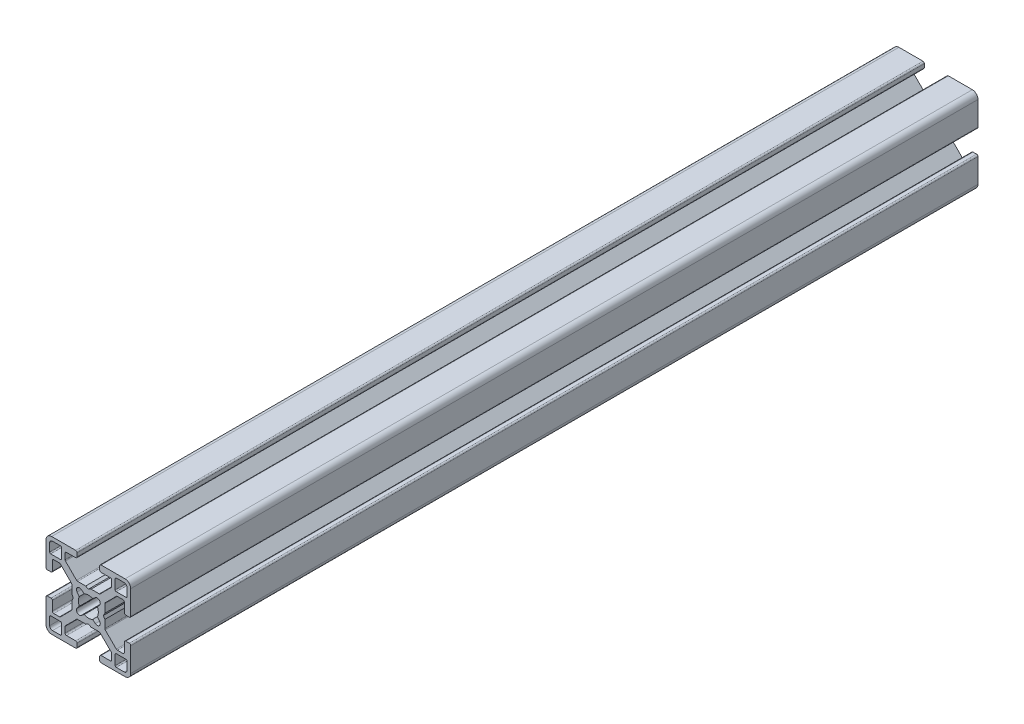
SolidWorks part; units mm, degrees
material "6105-T5 Aluminum"
ref_plane "Front Plane" through (0, 0, 0) normal (0, 0, 1) x (1, 0, 0)
ref_plane "Top Plane" through (0, 0, 0) normal (0, 1, 0) x (1, 0, 0)
ref_plane "Right Plane" through (0, 0, 0) normal (1, 0, 0) x (0, 0, -1)
sketch "Sketch1" plane through (0, 0, 0) normal (0, 0, 1) x (1, 0, 0)
  line L0 (9.5, -13.3189) -> (9.5, -9.88)
  line L1 (9.88, -9.5) -> (13.3189, -9.5)
  line L2 (13.6999, -9.881) -> (13.6999, -12.6999)
  line L3 (12.6999, -13.6999) -> (9.881, -13.6999)
  line L4 (-13.3189, -9.5) -> (-9.88, -9.5)
  line L5 (-9.5, -9.88) -> (-9.5, -13.3189)
  line L6 (-9.881, -13.6999) -> (-12.6999, -13.6999)
  line L7 (-13.6999, -12.6999) -> (-13.6999, -9.881)
  line L8 (-1.4942, -3.1981) -> (-2.4733, -3.9799)
  line L9 (-3.9799, -2.4733) -> (-3.1981, -1.4942)
  line L10 (-3.1981, 1.4942) -> (-3.9799, 2.4733)
  line L11 (-2.4733, 3.9799) -> (-1.4942, 3.1981)
  line L12 (1.4942, 3.1981) -> (2.4733, 3.9799)
  line L13 (3.9799, 2.4733) -> (3.1981, 1.4942)
  line L14 (3.1981, -1.4942) -> (3.9799, -2.4733)
  line L15 (2.4733, -3.9799) -> (1.4942, -3.1981)
  line L16 (-9.5, 13.3189) -> (-9.5, 9.88)
  line L17 (-9.88, 9.5) -> (-13.3189, 9.5)
  line L18 (-13.6999, 9.881) -> (-13.6999, 12.6999)
  line L19 (-12.6999, 13.6999) -> (-9.881, 13.6999)
  line L20 (9.881, 13.6999) -> (12.6999, 13.6999)
  line L21 (13.6999, 12.6999) -> (13.6999, 9.881)
  line L22 (13.3189, 9.5) -> (9.88, 9.5)
  line L23 (9.5, 9.88) -> (9.5, 13.3189)
  line L24 (12.7425, -4.5) -> (12.7425, -7.7325)
  line L25 (12.2428, -8.25) -> (10.2602, -8.25)
  line L26 (9.9066, -8.1035) -> (5.9811, -4.178)
  line L27 (5.8347, -3.8245) -> (5.8347, -1.0125)
  line L28 (5.8347, -1.0125) -> (5.3247, -0.0625)
  line L29 (5.3247, -0.0625) -> (5.8347, 0.8875)
  line L30 (5.8347, 0.8875) -> (5.8347, 3.8245)
  line L31 (5.9811, 4.178) -> (9.9066, 8.1035)
  line L32 (10.2602, 8.25) -> (12.2428, 8.25)
  line L33 (12.7425, 7.7325) -> (12.7425, 4.5)
  line L34 (13.2425, 4) -> (14.4999, 4)
  line L35 (14.9999, 4.5) -> (14.9999, 12.9999)
  line L36 (12.9999, 14.9999) -> (4.5, 14.9999)
  line L37 (4, 14.4999) -> (4, 13.2425)
  line L38 (4.5, 12.7425) -> (7.7325, 12.7425)
  line L39 (8.25, 12.2428) -> (8.25, 10.2602)
  line L40 (8.1035, 9.9066) -> (4.178, 5.9811)
  line L41 (3.8245, 5.8347) -> (0.95, 5.8347)
  line L42 (0.95, 5.8347) -> (0, 5.3247)
  line L43 (0, 5.3247) -> (-0.95, 5.8347)
  line L44 (-0.95, 5.8347) -> (-3.8245, 5.8347)
  line L45 (-4.178, 5.9811) -> (-8.1035, 9.9066)
  line L46 (-8.25, 10.2602) -> (-8.25, 12.2428)
  line L47 (-7.7325, 12.7425) -> (-4.5, 12.7425)
  line L48 (-4, 13.2425) -> (-4, 14.4999)
  line L49 (-4.5, 14.9999) -> (-12.9999, 14.9999)
  line L50 (-14.9999, 12.9999) -> (-14.9999, 4.5)
  line L51 (-14.4999, 4) -> (-13.2425, 4)
  line L52 (-12.7425, 4.5) -> (-12.7425, 7.7325)
  line L53 (-12.2428, 8.25) -> (-10.2602, 8.25)
  line L54 (-9.9066, 8.1035) -> (-5.9811, 4.178)
  line L55 (-5.8347, 3.8245) -> (-5.8347, 0.8875)
  line L56 (-5.8347, 0.8875) -> (-5.3247, -0.0625)
  line L57 (-5.3247, -0.0625) -> (-5.8347, -1.0125)
  line L58 (-5.8347, -1.0125) -> (-5.8347, -3.8245)
  line L59 (-5.9811, -4.178) -> (-9.9066, -8.1035)
  line L60 (-10.2602, -8.25) -> (-12.2428, -8.25)
  line L61 (-12.7425, -7.7325) -> (-12.7425, -4.5)
  line L62 (-13.2425, -4) -> (-14.4999, -4)
  line L63 (-14.9999, -4.5) -> (-14.9999, -12.9999)
  line L64 (-12.9999, -14.9999) -> (-4.5, -14.9999)
  line L65 (-4, -14.4999) -> (-4, -13.2425)
  line L66 (-4.5, -12.7425) -> (-7.7325, -12.7425)
  line L67 (-8.25, -12.2428) -> (-8.25, -10.2602)
  line L68 (-8.1035, -9.9066) -> (-4.178, -5.9811)
  line L69 (-3.8245, -5.8347) -> (-0.95, -5.8347)
  line L70 (-0.95, -5.8347) -> (0, -5.3247)
  line L71 (0, -5.3247) -> (0.95, -5.8347)
  line L72 (0.95, -5.8347) -> (3.8245, -5.8347)
  line L73 (4.178, -5.9811) -> (8.1035, -9.9066)
  line L74 (8.25, -10.2602) -> (8.25, -12.2428)
  line L75 (7.7325, -12.7425) -> (4.5, -12.7425)
  line L76 (4, -13.2425) -> (4, -14.4999)
  line L77 (4.5, -14.9999) -> (12.9999, -14.9999)
  line L78 (14.9999, -12.9999) -> (14.9999, -4.5)
  line L79 (14.4999, -4) -> (13.2425, -4)
  arc A0 (9.5, -13.3189) -> (9.881, -13.6999) centre (9.881, -13.3189) ccw
  arc A1 (9.88, -9.5) -> (9.5, -9.88) centre (9.88, -9.88) ccw
  arc A2 (13.6999, -9.881) -> (13.3189, -9.5) centre (13.3189, -9.881) ccw
  arc A3 (12.6999, -13.6999) -> (13.6999, -12.6999) centre (12.6999, -12.6999) ccw
  arc A4 (-13.3189, -9.5) -> (-13.6999, -9.881) centre (-13.3189, -9.881) ccw
  arc A5 (-9.5, -9.88) -> (-9.88, -9.5) centre (-9.88, -9.88) ccw
  arc A6 (-9.881, -13.6999) -> (-9.5, -13.3189) centre (-9.881, -13.3189) ccw
  arc A7 (-13.6999, -12.6999) -> (-12.6999, -13.6999) centre (-12.6999, -12.6999) ccw
  arc A8 (-1.4942, -3.1981) -> (1.4942, -3.1981) centre (0, 0) ccw
  arc A9 (-3.9799, -2.4733) -> (-2.4733, -3.9799) centre (-3.1422, -3.1422) ccw
  arc A10 (-3.1981, 1.4942) -> (-3.1981, -1.4942) centre (0, 0) ccw
  arc A11 (-2.4733, 3.9799) -> (-3.9799, 2.4733) centre (-3.1422, 3.1422) ccw
  arc A12 (1.4942, 3.1981) -> (-1.4942, 3.1981) centre (0, 0) ccw
  arc A13 (3.9799, 2.4733) -> (2.4733, 3.9799) centre (3.1422, 3.1422) ccw
  arc A14 (3.1981, -1.4942) -> (3.1981, 1.4942) centre (0, 0) ccw
  arc A15 (2.4733, -3.9799) -> (3.9799, -2.4733) centre (3.1422, -3.1422) ccw
  arc A16 (-9.5, 13.3189) -> (-9.881, 13.6999) centre (-9.881, 13.3189) ccw
  arc A17 (-9.88, 9.5) -> (-9.5, 9.88) centre (-9.88, 9.88) ccw
  arc A18 (-13.6999, 9.881) -> (-13.3189, 9.5) centre (-13.3189, 9.881) ccw
  arc A19 (-12.6999, 13.6999) -> (-13.6999, 12.6999) centre (-12.6999, 12.6999) ccw
  arc A20 (9.881, 13.6999) -> (9.5, 13.3189) centre (9.881, 13.3189) ccw
  arc A21 (13.6999, 12.6999) -> (12.6999, 13.6999) centre (12.6999, 12.6999) ccw
  arc A22 (13.3189, 9.5) -> (13.6999, 9.881) centre (13.3189, 9.881) ccw
  arc A23 (9.5, 9.88) -> (9.88, 9.5) centre (9.88, 9.88) ccw
  arc A24 (13.2425, -4) -> (12.7425, -4.5) centre (13.2425, -4.5) ccw
  arc A25 (12.2428, -8.25) -> (12.7425, -7.7325) centre (12.2428, -7.75) ccw
  arc A26 (9.9066, -8.1035) -> (10.2602, -8.25) centre (10.2602, -7.75) ccw
  arc A27 (5.8347, -3.8245) -> (5.9811, -4.178) centre (6.3347, -3.8245) ccw
  arc A28 (5.9811, 4.178) -> (5.8347, 3.8245) centre (6.3347, 3.8245) ccw
  arc A29 (10.2602, 8.25) -> (9.9066, 8.1035) centre (10.2602, 7.75) ccw
  arc A30 (12.7425, 7.7325) -> (12.2428, 8.25) centre (12.2428, 7.75) ccw
  arc A31 (12.7425, 4.5) -> (13.2425, 4) centre (13.2425, 4.5) ccw
  arc A32 (14.4999, 4) -> (14.9999, 4.5) centre (14.4999, 4.5) ccw
  arc A33 (14.9999, 12.9999) -> (12.9999, 14.9999) centre (12.9999, 12.9999) ccw
  arc A34 (4.5, 14.9999) -> (4, 14.4999) centre (4.5, 14.4999) ccw
  arc A35 (4, 13.2425) -> (4.5, 12.7425) centre (4.5, 13.2425) ccw
  arc A36 (8.25, 12.2428) -> (7.7325, 12.7425) centre (7.75, 12.2428) ccw
  arc A37 (8.1035, 9.9066) -> (8.25, 10.2602) centre (7.75, 10.2602) ccw
  arc A38 (3.8245, 5.8347) -> (4.178, 5.9811) centre (3.8245, 6.3347) ccw
  arc A39 (-4.178, 5.9811) -> (-3.8245, 5.8347) centre (-3.8245, 6.3347) ccw
  arc A40 (-8.25, 10.2602) -> (-8.1035, 9.9066) centre (-7.75, 10.2602) ccw
  arc A41 (-7.7325, 12.7425) -> (-8.25, 12.2428) centre (-7.75, 12.2428) ccw
  arc A42 (-4.5, 12.7425) -> (-4, 13.2425) centre (-4.5, 13.2425) ccw
  arc A43 (-4, 14.4999) -> (-4.5, 14.9999) centre (-4.5, 14.4999) ccw
  arc A44 (-12.9999, 14.9999) -> (-14.9999, 12.9999) centre (-12.9999, 12.9999) ccw
  arc A45 (-14.9999, 4.5) -> (-14.4999, 4) centre (-14.4999, 4.5) ccw
  arc A46 (-13.2425, 4) -> (-12.7425, 4.5) centre (-13.2425, 4.5) ccw
  arc A47 (-12.2428, 8.25) -> (-12.7425, 7.7325) centre (-12.2428, 7.75) ccw
  arc A48 (-9.9066, 8.1035) -> (-10.2602, 8.25) centre (-10.2602, 7.75) ccw
  arc A49 (-5.8347, 3.8245) -> (-5.9811, 4.178) centre (-6.3347, 3.8245) ccw
  arc A50 (-5.9811, -4.178) -> (-5.8347, -3.8245) centre (-6.3347, -3.8245) ccw
  arc A51 (-10.2602, -8.25) -> (-9.9066, -8.1035) centre (-10.2602, -7.75) ccw
  arc A52 (-12.7425, -7.7325) -> (-12.2428, -8.25) centre (-12.2428, -7.75) ccw
  arc A53 (-12.7425, -4.5) -> (-13.2425, -4) centre (-13.2425, -4.5) ccw
  arc A54 (-14.4999, -4) -> (-14.9999, -4.5) centre (-14.4999, -4.5) ccw
  arc A55 (-14.9999, -12.9999) -> (-12.9999, -14.9999) centre (-12.9999, -12.9999) ccw
  arc A56 (-4.5, -14.9999) -> (-4, -14.4999) centre (-4.5, -14.4999) ccw
  arc A57 (-4, -13.2425) -> (-4.5, -12.7425) centre (-4.5, -13.2425) ccw
  arc A58 (-8.25, -12.2428) -> (-7.7325, -12.7425) centre (-7.75, -12.2428) ccw
  arc A59 (-8.1035, -9.9066) -> (-8.25, -10.2602) centre (-7.75, -10.2602) ccw
  arc A60 (-3.8245, -5.8347) -> (-4.178, -5.9811) centre (-3.8245, -6.3347) ccw
  arc A61 (4.178, -5.9811) -> (3.8245, -5.8347) centre (3.8245, -6.3347) ccw
  arc A62 (8.25, -10.2602) -> (8.1035, -9.9066) centre (7.75, -10.2602) ccw
  arc A63 (7.7325, -12.7425) -> (8.25, -12.2428) centre (7.75, -12.2428) ccw
  arc A64 (4.5, -12.7425) -> (4, -13.2425) centre (4.5, -13.2425) ccw
  arc A65 (4, -14.4999) -> (4.5, -14.9999) centre (4.5, -14.4999) ccw
  arc A66 (12.9999, -14.9999) -> (14.9999, -12.9999) centre (12.9999, -12.9999) ccw
  arc A67 (14.9999, -4.5) -> (14.4999, -4) centre (14.4999, -4.5) ccw
extrude "Extrude1" add sketch "Sketch1" against normal blind 300
